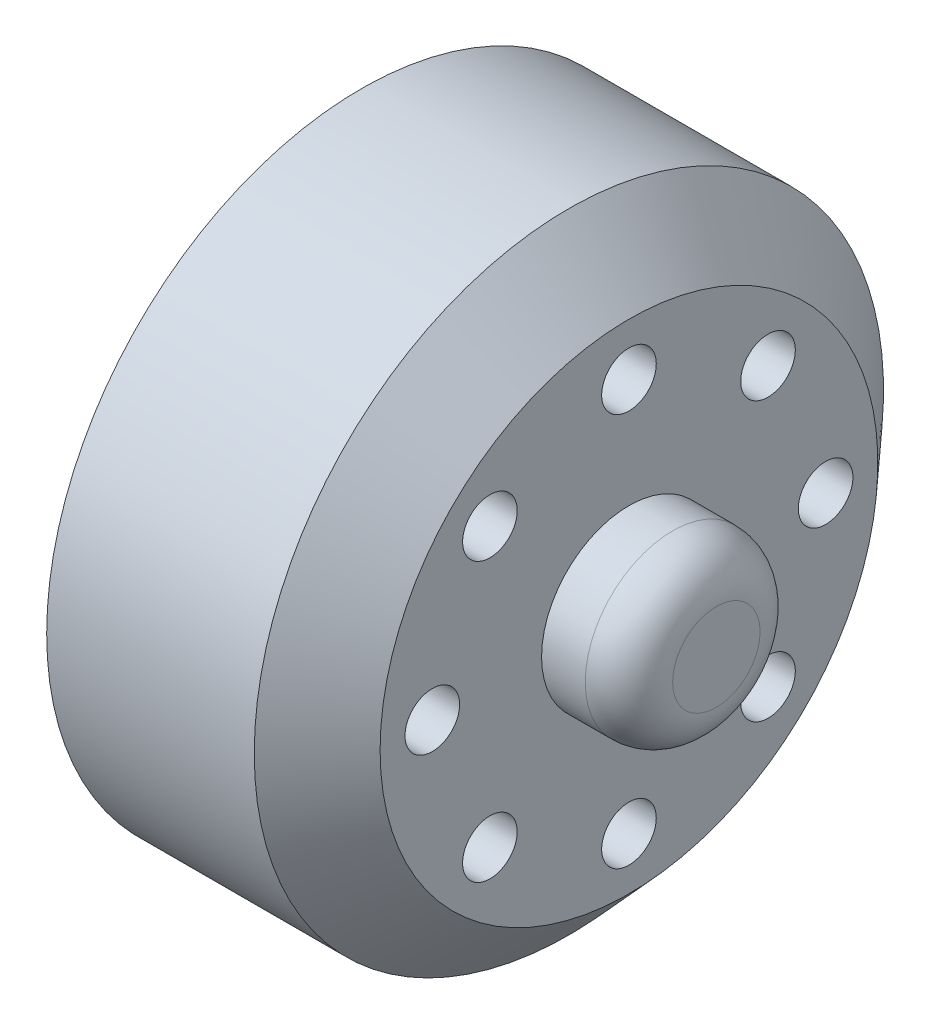
SolidWorks part; units mm, degrees
ref_plane "Front Plane" through (0, 0, 0) normal (0, 0, 1) x (1, 0, 0)
ref_plane "Top Plane" through (0, 0, 0) normal (0, 1, 0) x (1, 0, 0)
ref_plane "Right Plane" through (0, 0, 0) normal (1, 0, 0) x (0, 0, -1)
sketch "Sketch1" plane through (0, 0, 0) normal (0, 1, 0) x (1, 0, 0)
  line L0 (-12.3913, 0) -> (21, 0) construction
  line L1 (-1.6304, 14.4) -> (7.8696, 14.4)
  line L5 (13.3727, 0) -> (3.0717, 0)
  line L8 (10.6196, 4) -> (14.6196, 4)
  line L9 (14.6196, 4) -> (14.6196, 0)
  line L10 (14.6196, 0) -> (13.3727, 0)
  line L15 (7.8696, 14.4) -> (10.6196, 11.3905)
  line L17 (10.6196, 11.3905) -> (10.6196, 4)
  line L18 (-1.6304, 14.4) -> (-1.6304, 5.7)
  line L20 (3.0717, 5.7) -> (3.0717, 0)
  line L21 (3.0717, 5.7) -> (-1.6304, 5.7)
  dimension "D2" = 132.42
  dimension "D3" = 4.0767
  dimension "D4" = 9.5
  dimension "D5" = 28.8
  dimension "D6" = 3.0095
  dimension "D7" = 4
  dimension "D8" = 8
  dimension "D10" = 11.4
  dimension "D11" = 11.3905
  dimension "D12" = 12.25
revolve "Revolve1" add sketch "Sketch1" angle 360 about L0
fillet "Fillet1" radius 2 1 edges at (14.6196, 0, 4)
sketch "Sketch2" plane through (10.6196, 0, 0) normal (1, 0, 0) x (0, 0, -1)
  circle A0 centre (0, 0) radius 9 construction
  circle A1 centre (0, 9) radius 1.25
  circle A2 centre (6.364, 6.364) radius 1.25
  circle A3 centre (9, 0) radius 1.25
  circle A4 centre (6.364, -6.364) radius 1.25
  circle A5 centre (0, -9) radius 1.25
  circle A6 centre (-6.364, -6.364) radius 1.25
  circle A7 centre (-9, 0) radius 1.25
  circle A8 centre (-6.364, 6.364) radius 1.25
  point P22 (0, 0)
  dimension "D1" = 18
  dimension "D2" = 2.5
  dimension "D3" = 8
extrude "Cut-Extrude1" cut sketch "Sketch2" against normal up to surface (12.25 mm away) up to face at (-1.6304, 0, 5.7)
sketch "Sketch3" plane through (-1.6304, 0, 0) normal (-1, 0, 0) x (0, 0, 1)
  circle A0 centre (0, 0) radius 9 construction
  circle A1 centre (0, 9) radius 2.5
  circle A2 centre (6.364, 6.364) radius 2.5
  circle A3 centre (9, 0) radius 2.5
  circle A4 centre (6.364, -6.364) radius 2.5
  circle A5 centre (0, -9) radius 2.5
  circle A6 centre (-6.364, -6.364) radius 2.5
  circle A7 centre (-9, 0) radius 2.5
  circle A8 centre (-6.364, 6.364) radius 2.5
  point P22 (0, 0)
  dimension "D1" = 18
  dimension "D2" = 5
  dimension "D3" = 8
extrude "Cut-Extrude2" cut sketch "Sketch3" against normal offset from surface (7.25 mm away) 5 up to face at (10.6196, 9, -1.25)
